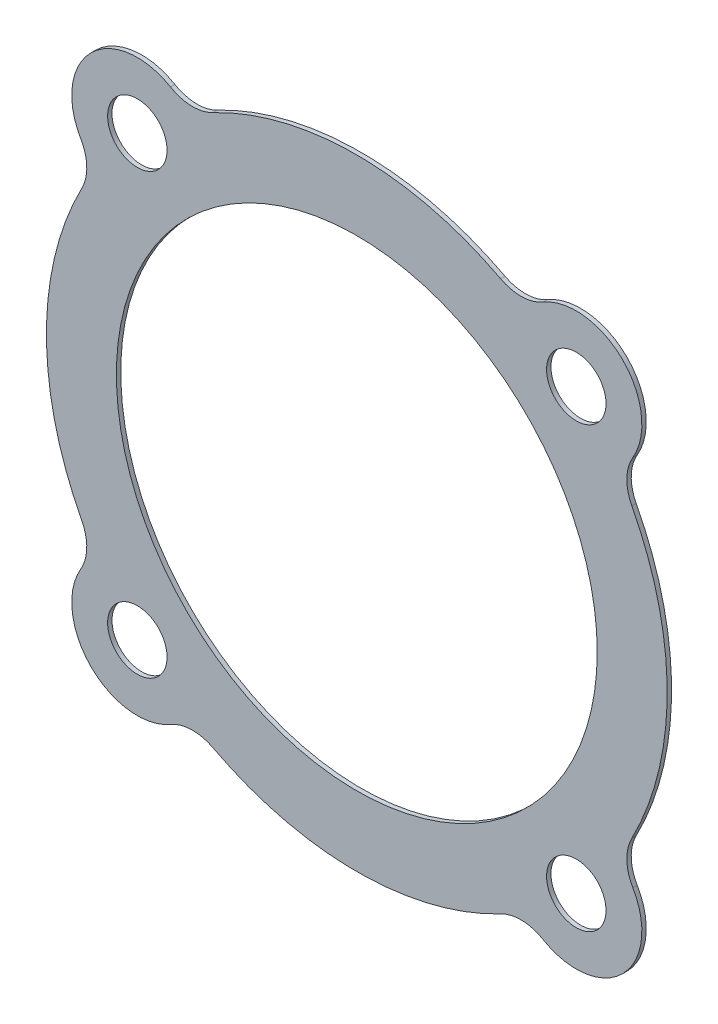
SolidWorks part; units mm, degrees
material "VITON"
ref_plane "Front Plane" through (0, 0, 0) normal (0, 0, 1) x (1, 0, 0)
ref_plane "Top Plane" through (0, 0, 0) normal (0, 1, 0) x (1, 0, 0)
ref_plane "Right Plane" through (0, 0, 0) normal (1, 0, 0) x (0, 0, -1)
sketch "Sketch1" plane through (0, 0, 0) normal (0, 0, 1) x (1, 0, 0)
  line L0 (0, 0) -> (31.8799, 31.8799) construction
  line L1 (0, 0) -> (45.085, 0) construction
  line L2 (0, 45.085) -> (0, -45.085) construction
  line L3 (0, 0) -> (-45.085, 0) construction
  circle A0 centre (0, 0) radius 34.925
  arc A1 (20.9031, 39.9464) -> (-20.9031, 39.9464) centre (0, 0) ccw
  circle A2 centre (31.8799, 31.8799) radius 4.318
  arc A3 (40.0956, 27.0603) -> (27.0603, 40.0956) centre (31.8799, 31.8799) ccw
  arc A4 (39.9464, 20.9031) -> (40.0956, 27.0603) centre (45.5727, 23.8472) cw
  arc A5 (20.9031, 39.9464) -> (27.0603, 40.0956) centre (23.8472, 45.5727) ccw
  arc A6 (20.9031, -39.9464) -> (27.0603, -40.0956) centre (23.8472, -45.5727) cw
  arc A7 (39.9464, -20.9031) -> (40.0956, -27.0603) centre (45.5727, -23.8472) ccw
  arc A8 (40.0956, -27.0603) -> (27.0603, -40.0956) centre (31.8799, -31.8799) cw
  circle A9 centre (31.8799, -31.8799) radius 4.318
  arc A10 (39.9464, -20.9031) -> (39.9464, 20.9031) centre (0, 0) ccw
  circle A11 centre (-31.8799, -31.8799) radius 4.318
  arc A12 (-40.0956, -27.0603) -> (-27.0603, -40.0956) centre (-31.8799, -31.8799) ccw
  arc A13 (-39.9464, -20.9031) -> (-40.0956, -27.0603) centre (-45.5727, -23.8472) cw
  arc A14 (-20.9031, -39.9464) -> (-27.0603, -40.0956) centre (-23.8472, -45.5727) ccw
  arc A15 (-20.9031, 39.9464) -> (-27.0603, 40.0956) centre (-23.8472, 45.5727) cw
  arc A16 (-39.9464, 20.9031) -> (-40.0956, 27.0603) centre (-45.5727, 23.8472) ccw
  arc A17 (-40.0956, 27.0603) -> (-27.0603, 40.0956) centre (-31.8799, 31.8799) cw
  circle A18 centre (-31.8799, 31.8799) radius 4.318
  arc A19 (-39.9464, 20.9031) -> (-39.9464, -20.9031) centre (0, 0) ccw
  arc A20 (-20.9031, -39.9464) -> (20.9031, -39.9464) centre (0, 0) ccw
  dimension "D1" = 69.85
  dimension "D2" = 90.17
  dimension "D4" = 8.636
  dimension "D5" = 19.05
  dimension "D6" = 6.35
  dimension "D7" = 6.35
  dimension "D3" = 45
extrude "Boss-Extrude1" add sketch "Sketch1" along normal blind 0.635
